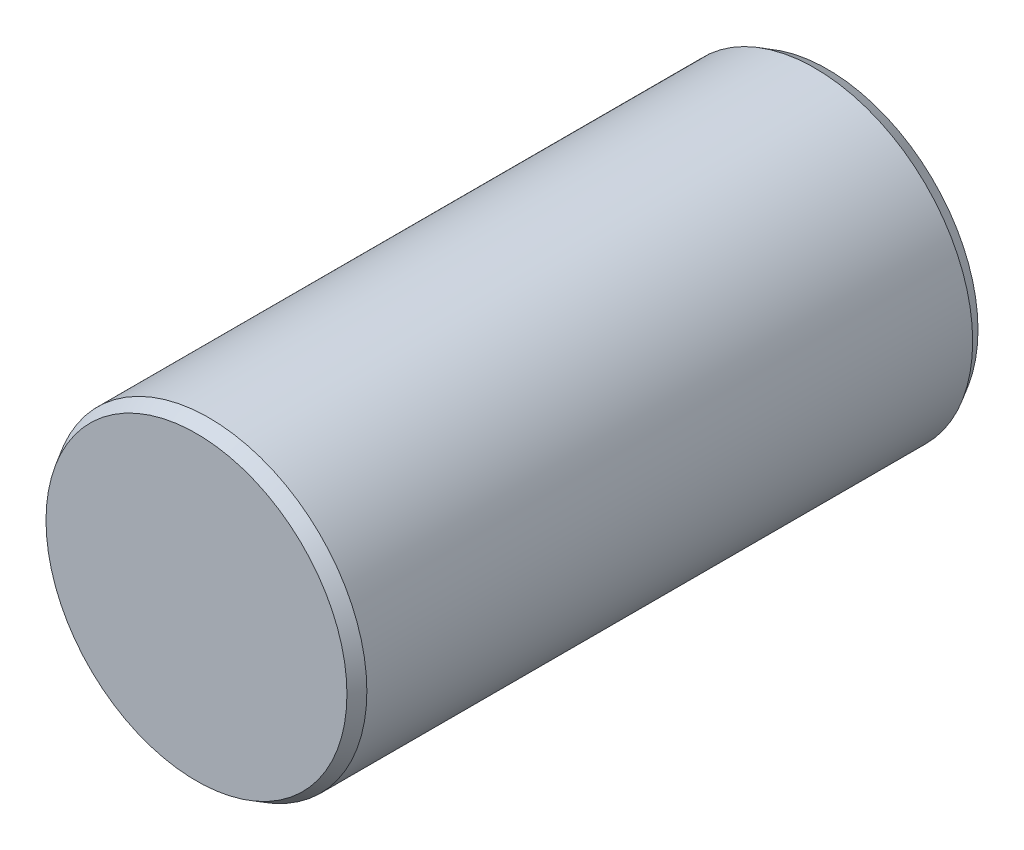
SolidWorks part; units mm, degrees
ref_plane "Plan de face" through (0, 0, 0) normal (0, 0, 1) x (1, 0, 0)
ref_plane "Plan de dessus" through (0, 0, 0) normal (0, 1, 0) x (1, 0, 0)
ref_plane "Plan de droite" through (0, 0, 0) normal (1, 0, 0) x (0, 0, -1)
sketch "Esquisse1" plane through (0, 0, 0) normal (0, 0, 1) x (1, 0, 0)
  circle A0 centre (0, 0) radius 2.5
  dimension "D1" = 5
extrude "Boss.-Extru.1" add sketch "Esquisse1" along normal mid plane 10
chamfer "Chanfrein1" distance 0.2 angle 30 2 edges at (2.5, 0, -5) (2.5, 0, 5)
